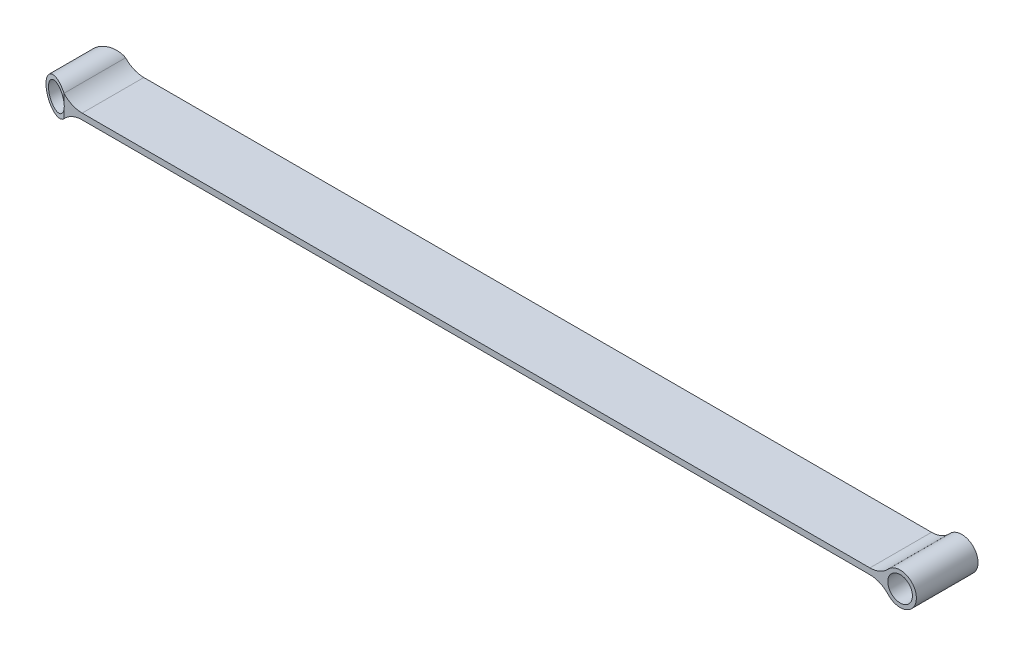
SolidWorks part; units mm, degrees
ref_plane "Front Plane" through (0, 0, 0) normal (0, 0, 1) x (1, 0, 0)
ref_plane "Top Plane" through (0, 0, 0) normal (0, 1, 0) x (1, 0, 0)
ref_plane "Right Plane" through (0, 0, 0) normal (1, 0, 0) x (0, 0, -1)
sketch "Sketch1" plane through (0, 0, 0) normal (0, 1, 0) x (1, 0, 0)
  line L1 (-101.6, -7.9375) -> (101.6, -7.9375)
  line L2 (-101.6, -7.9375) -> (-101.6, 7.9375)
  line L3 (-101.6, 7.9375) -> (101.6, 7.9375)
  line L4 (101.6, -7.9375) -> (101.6, 7.9375)
  line L5 (-101.6, -7.9375) -> (101.6, 7.9375) construction
  line L6 (-101.6, 7.9375) -> (101.6, -7.9375) construction
  point P0 (0, 0)
  dimension "D1" = 15.875
  dimension "D2" = 203.2
extrude "Boss-Extrude1" add sketch "Sketch1" along normal blind 1.524
sketch "Sketch4" plane through (0, 1.524, 0) normal (0, 1, 0) x (1, 0, 0)
  line L0 (-101.6, 7.9375) -> (-101.6, -7.9375) construction
  circle A0 centre (59.563, 0) radius 2.3812
  dimension "D1" = 161.163
  dimension "D2" = 4.7625
sketch "Sketch5" plane through (0, 0, 7.9375) normal (0, 0, 1) x (1, 0, 0)
  line L0 (-101.6, 0) -> (101.6, 0) construction
  line L1 (-101.6, 1.524) -> (101.6, 1.524) construction
  line L2 (-101.4398, 0) -> (101.6, 0)
  line L3 (-101.4398, 1.524) -> (101.6, 1.524)
  line L4 (-101.6, 1.524) -> (-101.6, 0) construction
  line L5 (-101.6, 1.524) -> (-101.6, 0)
  line L6 (101.6, 1.524) -> (101.6, 0)
  line L7 (-101.4398, 1.524) -> (-101.4398, 0)
  circle A0 centre (-109.22, 0.762) radius 3.175
  arc A1 (-106.1267, 3.5897) -> (-106.1267, -2.0657) centre (-109.22, 0.762) ccw
  circle A2 centre (-109.22, 0.762) radius 4.191 construction
  arc A3 (-101.4398, 1.524) -> (-106.1267, 3.5897) centre (-101.4398, 7.874) cw
  arc A4 (-106.1267, -2.0657) -> (-101.4398, 0) centre (-101.4398, -6.35) cw
  point P7 (-101.6, 0.762)
  line M5 (-101.6, 0) -> (101.6, 0)
  line M12 (101.6, 1.524) -> (-101.6, 1.524)
  line M13 (-101.6, 1.524) -> (-101.6, 0)
  dimension "D1" = 6.35
  dimension "D3" = 6.35
  dimension "D4" = 6.35
  dimension "D5" = 7.62
  dimension "D2" = 1.016
extrude "Boss-Extrude5" add sketch "Sketch5" against normal through all contours A1 A4 A3 A0 M5 M13 M12
mirror "Mirror1" about plane through (0, 0, 0) normal (1, 0, 0) of "Boss-Extrude5"
sketch "Sketch6" plane through (0, 0, 0) normal (0, -1, 0) x (1, 0, 0)
  line L0 (-113.411, 7.9375) -> (-113.411, -7.9375) construction
  line L1 (-113.411, -7.9375) -> (-106.1267, -7.9375) construction
  line L3 (101.4398, -7.9375) -> (-101.4398, -7.9375) construction
  line L4 (-101.4398, 7.9375) -> (101.4398, 7.9375) construction
  line L5 (-101.4398, 7.9375) -> (-106.1267, 7.9375) construction
  line L6 (-106.1267, 7.9375) -> (-113.411, 7.9375) construction
  line L7 (-113.411, 7.9375) -> (-113.411, 5.2862)
  line L8 (-113.411, -7.9375) -> (-106.1267, -7.9375)
  line L9 (-113.411, -7.9375) -> (-113.411, -5.2862)
  line L10 (101.4398, -7.9375) -> (-101.4398, -7.9375)
  line L11 (-101.4398, 7.9375) -> (101.4398, 7.9375)
  line L12 (-101.4398, 7.9375) -> (-106.1267, 7.9375)
  line L13 (-106.1267, 7.9375) -> (-113.411, 7.9375)
  line L14 (-113.411, 5.2862) -> (-106.1267, 7.9375)
  line L16 (-113.411, 0) -> (-106.1267, 0) construction
  line L17 (-106.1267, -7.9375) -> (-106.1267, 7.9375) construction
  line L18 (-106.1267, -7.9375) -> (-113.411, -7.9375)
  line L19 (-113.411, -7.9375) -> (-113.411, -5.2862)
  line L20 (-113.411, -5.2862) -> (-106.1267, -7.9375)
  dimension "D1" = 20
extrude "Cut-Extrude1" cut sketch "Sketch6" against normal through all and the other way through all contours L20 L9 L8 | L7 L14 L13
